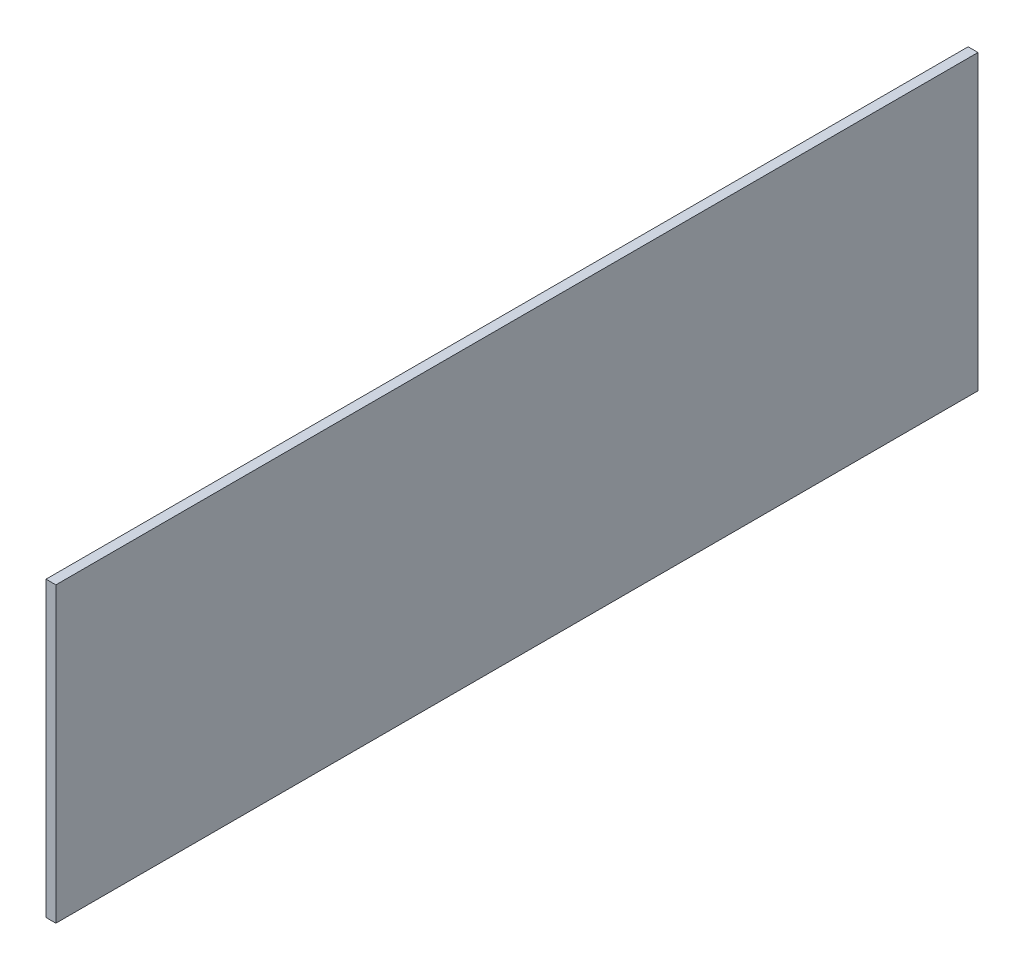
SolidWorks part; units mm, degrees
ref_plane "Front Plane" through (0, 0, 0) normal (0, 0, 1) x (1, 0, 0)
ref_plane "Top Plane" through (0, 0, 0) normal (0, 1, 0) x (1, 0, 0)
ref_plane "Right Plane" through (0, 0, 0) normal (1, 0, 0) x (0, 0, -1)
sketch "Sketch1" plane through (0, 0, 0) normal (1, 0, 0) x (0, 0, -1)
  line L1 (0, 0) -> (279.7556, 0)
  line L2 (0, 0) -> (0, -88.9)
  line L3 (0, -88.9) -> (279.7556, -88.9)
  line L4 (279.7556, 0) -> (279.7556, -88.9)
  dimension "D1" = 279.7556
  dimension "D2" = 88.9
extrude "Boss-Extrude1" add sketch "Sketch1" along normal blind 2.9972
